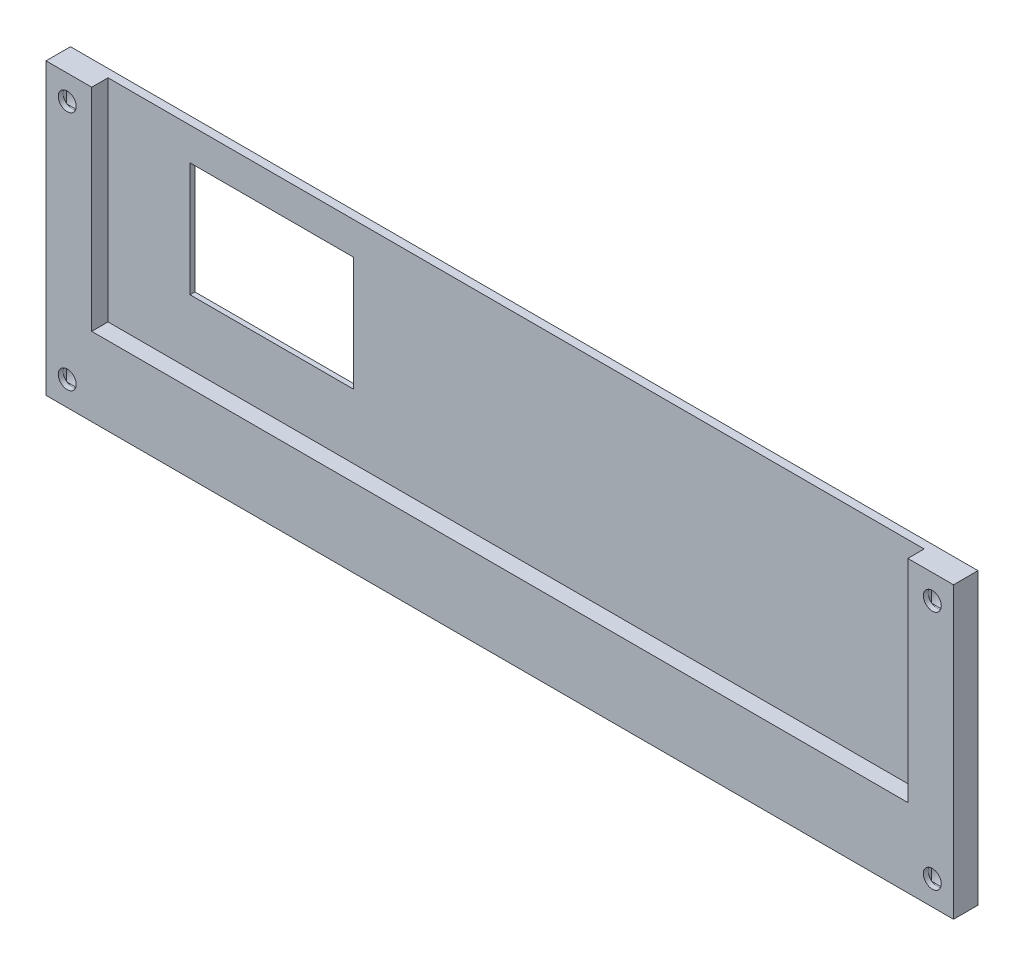
SolidWorks part; units mm, degrees
ref_plane "Front Plane" through (0, 0, 0) normal (0, 0, 1) x (1, 0, 0)
ref_plane "Top Plane" through (0, 0, 0) normal (0, 1, 0) x (1, 0, 0)
ref_plane "Right Plane" through (0, 0, 0) normal (1, 0, 0) x (0, 0, -1)
sketch "Sketch1" plane through (0, 0, 0) normal (0, 0, 1) x (1, 0, 0)
  line L1 (-56, -17.75) -> (56, -17.75)
  line L2 (-56, -17.75) -> (-56, 17.75)
  line L3 (-56, 17.75) -> (56, 17.75)
  line L4 (56, -17.75) -> (56, 17.75)
  line L5 (-56, -17.75) -> (56, 17.75) construction
  line L6 (-56, 17.75) -> (56, -17.75) construction
  point P0 (0, 0)
  dimension "D1" = 112
  dimension "D2" = 35.5
extrude "Boss-Extrude1" add sketch "Sketch1" along normal blind 1
sketch "Sketch2" plane through (0, 0, 1) normal (0, 0, 1) x (1, 0, 0)
  line L0 (0, 17.75) -> (0, -17.75) construction
  line L1 (-56, 17.75) -> (-50, 17.75)
  line L2 (-56, 17.75) -> (-56, 11.75)
  line L3 (-56, 11.75) -> (-50, 11.75)
  line L4 (-50, 17.75) -> (-50, 11.75)
  line L5 (-56, -17.75) -> (-50, -17.75)
  line L6 (-56, -17.75) -> (-56, -11.75)
  line L7 (-56, -11.75) -> (-50, -11.75)
  line L8 (-50, -17.75) -> (-50, -11.75)
  line L9 (56, 17.75) -> (-56, 17.75) construction
  line L10 (-56, -17.75) -> (56, -17.75) construction
  line L11 (50, -17.75) -> (50, -11.75)
  line L12 (56, -11.75) -> (50, -11.75)
  line L13 (56, -17.75) -> (56, -11.75)
  line L14 (56, -17.75) -> (50, -17.75)
  line L15 (50, 17.75) -> (50, 11.75)
  line L16 (56, 11.75) -> (50, 11.75)
  line L17 (56, 17.75) -> (56, 11.75)
  line L18 (56, 17.75) -> (50, 17.75)
  dimension "D1" = 6
extrude "Boss-Extrude2" add sketch "Sketch2" along normal blind 2
sketch "Sketch3" plane through (0, 0, 3) normal (0, 0, 1) x (1, 0, 0)
  line L0 (-50, 11.75) -> (-56, 17.75) construction
  line L1 (-50, -11.75) -> (-56, -17.75) construction
  line L2 (50, -11.75) -> (56, -17.75) construction
  line L3 (-56, 0) -> (56, 0) construction
  line L4 (-56, 11.75) -> (-56, -11.75) construction
  line L5 (56, -11.75) -> (56, 11.75) construction
  line L6 (0, 17.75) -> (0, -17.75) construction
  line L7 (50, 17.75) -> (-50, 17.75) construction
  line L8 (-50, -17.75) -> (50, -17.75) construction
  line L9 (50, 11.75) -> (56, 17.75) construction
  circle A0 centre (-53, 14.75) radius 1.1
  circle A1 centre (-53, -14.75) radius 1.1
  circle A2 centre (53, -14.75) radius 1.1
  circle A3 centre (53, 14.75) radius 1.1
  dimension "D1" = 2.2
extrude "Cut-Extrude1" cut sketch "Sketch3" against normal through all
sketch "Sketch4" plane through (0, 0, 0) normal (0, 0, -1) x (-1, 0, 0)
  circle A0 centre (-53, 14.75) radius 2
  circle A1 centre (-53, -14.75) radius 2
  circle A2 centre (53, 14.75) radius 2
  circle A3 centre (53, -14.75) radius 2
  dimension "D1" = 4
extrude "Cut-Extrude2" cut sketch "Sketch4" against normal blind 2
sketch "Sketch5" plane through (0, 0, 0) normal (0, 0, -1) x (-1, 0, 0)
  line L0 (-56, 17.75) -> (56, 17.75) construction
  line L1 (19.95, -0.25) -> (39.95, -0.25)
  line L2 (19.95, -0.25) -> (19.95, 13.75)
  line L3 (19.95, 13.75) -> (39.95, 13.75)
  line L4 (39.95, -0.25) -> (39.95, 13.75)
  line L5 (19.95, -0.25) -> (39.95, 13.75) construction
  line L6 (19.95, 13.75) -> (39.95, -0.25) construction
  line L7 (56, 17.75) -> (56, -17.75) construction
  point P0 (29.95, 6.75)
  dimension "D1" = 20
  dimension "D2" = 14
  dimension "D3" = 4
  dimension "D4" = 16.05
extrude "Cut-Extrude3" cut sketch "Sketch5" against normal through all
chamfer "Chamfer1" distance 0.4 angle 45 4 edges at (-29.95, 13.75, 0) (-19.95, 6.75, 0) (-29.95, -0.25, 0) (-39.95, 6.75, 0)
sketch "Sketch6" plane through (0, 0, 2) normal (0, 0, -1) x (-1, 0, 0)
  line L2 (-54.1, 13.0797) -> (-54.1, 16.4203)
  line L4 (-51.9, 13.0797) -> (-51.9, 16.4203)
  line L5 (-54.1, 13.0797) -> (-51.9, 16.4203) construction
  line L6 (-54.1, 16.4203) -> (-51.9, 13.0797) construction
  circle A0 centre (-53, 14.75) radius 2 construction
  circle A1 centre (-53, 14.75) radius 1.1 construction
  circle A2 centre (-53, 14.75) radius 2 construction
  arc A3 (-51.9, 16.4203) -> (-54.1, 16.4203) centre (-53, 14.75) ccw
  arc A4 (-54.1, 13.0797) -> (-51.9, 13.0797) centre (-53, 14.75) ccw
  point P0 (-53, 14.75)
extrude "Cut-Extrude4" cut sketch "Sketch6" against normal blind 0.2
sketch "Sketch7" plane through (0, 0, 2.2) normal (0, 0, -1) x (-1, 0, 0)
  line L0 (-51.9, 14.75) -> (-51.9, 16.4203) construction
  line L1 (-54.1, 13.65) -> (-51.9, 13.65)
  line L2 (-54.1, 13.65) -> (-54.1, 15.85)
  line L3 (-54.1, 15.85) -> (-51.9, 15.85)
  line L4 (-51.9, 13.65) -> (-51.9, 15.85)
  line L5 (-54.1, 13.65) -> (-51.9, 15.85) construction
  line L6 (-54.1, 15.85) -> (-51.9, 13.65) construction
  arc A0 (-51.9, 14.75) -> (-54.1, 14.75) centre (-53, 14.75) ccw construction
  point P0 (-53, 14.75)
extrude "Cut-Extrude5" cut sketch "Sketch7" against normal blind 0.2
mirror "Mirror1" about plane through (0, 0, 0) normal (1, 0, 0) of "Cut-Extrude4", "Cut-Extrude5"
mirror "Mirror2" about plane through (0, 0, 0) normal (0, 1, 0) of "Mirror1", "Cut-Extrude4", "Cut-Extrude5"
sketch "Sketch8" plane through (0, 0, 1) normal (0, 0, 1) x (1, 0, 0)
  line L0 (-56, -17.75) -> (-50, -17.75) construction
  line L1 (-56, 17.75) -> (-55.6, 17.75)
  line L2 (-56, 17.75) -> (-56, -17.75)
  line L3 (-56, -17.75) -> (-55.6, -17.75)
  line L4 (-55.6, 17.75) -> (-55.6, -17.75)
  line L5 (50, -17.75) -> (56, -17.75) construction
  line L6 (56, 17.75) -> (55.6, 17.75)
  line L7 (56, 17.75) -> (56, -17.75)
  line L8 (56, -17.75) -> (55.6, -17.75)
  line L9 (55.6, 17.75) -> (55.6, -17.75)
  dimension "D1" = 0.4
extrude "Cut-Extrude6" cut sketch "Sketch8" against normal through all both and the other way through all
sketch "Skizze1" plane through (0, 0, 1) normal (0, 0, 1) x (1, 0, 0)
  line L0 (-50, 11.75) -> (-50, -11.75)
  line L2 (-50, -11.75) -> (-55.6, -11.75)
  line L4 (-55.6, -11.75) -> (-55.6, 11.75)
  line L5 (-55.6, 11.75) -> (-50, 11.75)
  line L6 (50, 11.75) -> (50, -11.75)
  line L7 (55.6, -11.75) -> (50, -11.75) construction
  line L8 (50, -11.75) -> (55.6, -11.75)
  line L11 (55.6, -11.75) -> (55.6, 11.75)
  line L12 (55.6, 11.75) -> (50, 11.75)
  line L14 (-50, -8.1568) -> (50, -8.1568)
  line L15 (-50, -8.1568) -> (-50, -17.75)
  line L16 (-50, -17.75) -> (50, -17.75)
  line L17 (50, -8.1568) -> (50, -17.75)
  point P4 (-12.8979, -11.75)
  line M19 (-50, 11.75) -> (-55.6, 11.75)
  line M20 (-55.6, 11.75) -> (-55.6, -11.75)
  line M21 (-55.6, -11.75) -> (-50, -11.75)
  line M22 (-50, -11.75) -> (-50, -17.75)
  line M23 (-50, -17.75) -> (50, -17.75)
  line M24 (50, -17.75) -> (50, -11.75)
  line M25 (50, -11.75) -> (55.6, -11.75)
  line M26 (55.6, -11.75) -> (55.6, 11.75)
  line M27 (55.6, 11.75) -> (50, 11.75)
extrude "Aufsatz-Linear austragen1" add sketch "Skizze1" along normal up to surface (2 mm away) contours L14 L0 L6 M22 M23 M24 | L0 M19 M20 M21 | L6 M27 M25 M26 up to face at (-52.8, 14.75, 3)
